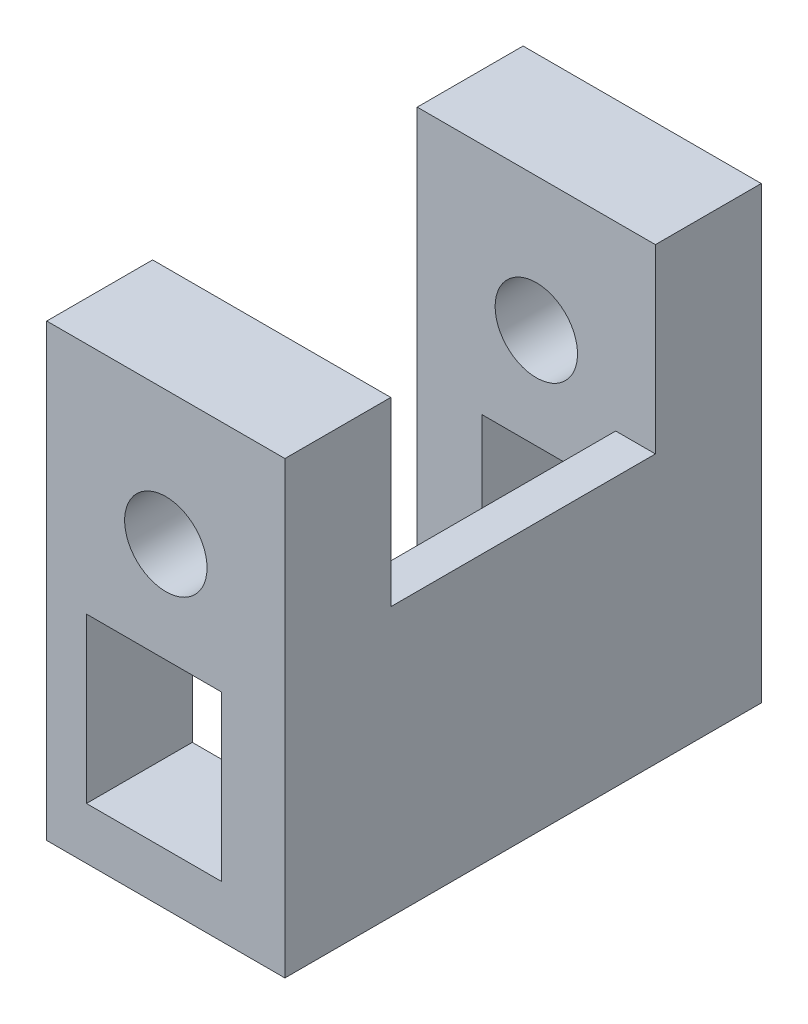
SolidWorks part; units mm, degrees
ref_plane "Ebene vorne" through (0, 0, 0) normal (0, 0, 1) x (1, 0, 0)
ref_plane "Ebene oben" through (0, 0, 0) normal (0, 1, 0) x (1, 0, 0)
ref_plane "Ebene rechts" through (0, 0, 0) normal (1, 0, 0) x (0, 0, -1)
sketch "Skizze3" plane through (0, 0, -22.0614) normal (0, 0, -1) x (-1, 0, 0)
  line L0 (-14.1061, 1.4246) -> (-5.1061, 1.4246)
  line L1 (-5.1061, -8.7256) -> (-5.1061, 8.2744) construction
  line L2 (-5.1061, 1.4246) -> (-5.1061, -8.7256)
  line L3 (-5.1061, -8.7256) -> (-14.1061, -8.7256)
  line L4 (-14.1061, -8.7256) -> (-14.1061, 1.4246)
  line L6 (-9.1556, -0.5644) -> (-9.1556, -6.9) construction
  line L7 (-10.7556, -0.5644) -> (-10.7556, -6.9) construction
  line L8 (-7.5556, -0.5644) -> (-7.5556, -6.9) construction
  line L9 (-7.5556, -0.5644) -> (-10.7556, -0.5644)
  line L10 (-9.605, -0.5644) -> (-11.705, -0.5644) construction
  line L11 (-10.7556, -0.5644) -> (-10.7556, -6.7644)
  line L12 (-11.705, -6.7644) -> (-9.605, -6.7644) construction
  line L13 (-10.7556, -6.7644) -> (-7.5556, -6.7644)
  line L14 (-7.5556, -6.7644) -> (-7.5556, -0.5644)
extrude "Aufsatz-Linear austragen2" add sketch "Skizze3" along normal blind 4
sketch "Skizze4" plane through (0, 0, -22.0614) normal (0, 0, 1) x (1, 0, 0)
  line L0 (12.6053, 1.4246) -> (14.1061, 1.4246)
  line L1 (5.1061, 1.4246) -> (14.1061, 1.4246) construction
  line L2 (14.1061, 1.4246) -> (14.1061, -8.7256)
  line L3 (14.1061, -8.7256) -> (12.6061, -8.7256)
  line L4 (14.1061, -8.7256) -> (5.1061, -8.7256) construction
  line L5 (12.6061, 1.4246) -> (12.6061, -8.7256) construction
  line L6 (12.6061, -8.7256) -> (12.6053, 1.4246)
extrude "Aufsatz-Linear austragen3" add sketch "Skizze4" along normal blind 10
sketch "Skizze6" plane through (0, 0, -22.0614) normal (0, 0, -1) x (-1, 0, 0)
  line L0 (-14.1061, 1.4246) -> (-5.1061, 1.4246)
  line L1 (-14.1061, 1.4246) -> (-12.6061, 1.4246) construction
  line L2 (-5.1061, 1.4246) -> (-5.1061, 8.2744)
  line L3 (-5.1061, 8.2744) -> (-14.1061, 8.2744)
  line L4 (-14.1061, 8.2744) -> (-14.1061, 1.4246)
extrude "Aufsatz-Linear austragen5" add sketch "Skizze6" along normal blind 4
sketch "Skizze7" plane through (0, 0, -26.0614) normal (0, 0, -1) x (-1, 0, 0)
  circle A0 centre (-9.6061, 3.2241) radius 1.5569
extrude "Schnitt-Linear austragen1" cut sketch "Skizze7" against normal blind 4
sketch "Skizze8" plane through (0, 0, -12.0614) normal (0, 0, 1) x (1, 0, 0)
  line L0 (5.1061, 8.2744) -> (14.1061, 8.2744)
  line L1 (14.1061, 8.2744) -> (14.1061, -8.7256)
  line L2 (14.1061, -8.7256) -> (5.1061, -8.7256)
  line L3 (5.1061, -8.7256) -> (5.1061, 8.2744)
  line L4 (6.6061, -0.5644) -> (11.705, -0.5644)
  line L5 (11.705, -0.5644) -> (11.705, -6.7644)
  line L6 (11.705, -6.7644) -> (6.6061, -6.7644)
  line L7 (6.6061, -6.7644) -> (6.6061, -0.5644)
  circle A0 centre (9.6061, 3.2241) radius 1.5569
extrude "Aufsatz-Linear austragen6" add sketch "Skizze8" along normal blind 4
